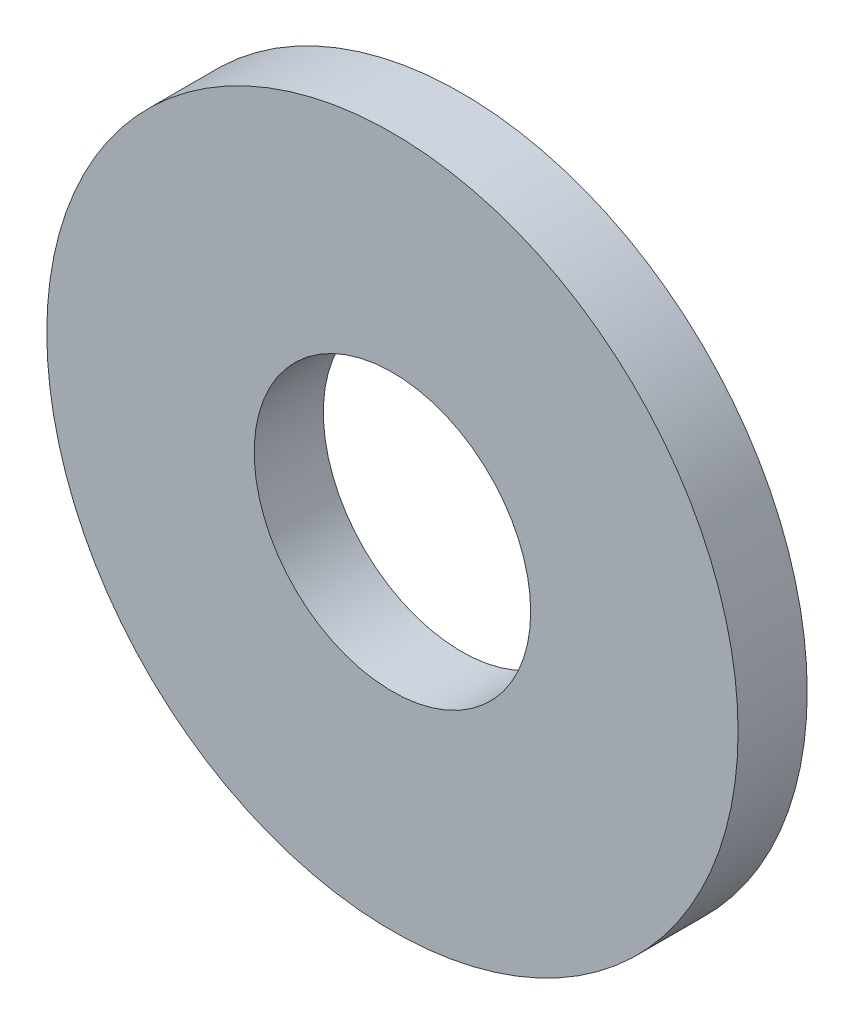
SolidWorks part; units mm, degrees
material "Nylon 6/10"
ref_plane "Front Plane" through (0, 0, 0) normal (0, 0, 1) x (1, 0, 0)
ref_plane "Top Plane" through (0, 0, 0) normal (0, 1, 0) x (1, 0, 0)
ref_plane "Right Plane" through (0, 0, 0) normal (1, 0, 0) x (0, 0, -1)
sketch "Sketch1" plane through (0, 0, 0) normal (0, 0, 1) x (1, 0, 0)
  circle A0 centre (0, 0) radius 4 construction
  circle A1 centre (0, 0) radius 1.6 construction
  point P5 (-1.6, 0)
  point P6 (1.6, 0)
  point P7 (4, 0)
  point P8 (-4, 0)
  dimension "OD" = 8
  dimension "ID" = 3.2
sketch "Sketch2" plane through (0, 0, 0) normal (1, 0, 0) x (0, 0, -1)
  line L0 (0.4, 0) -> (-0.4, 0) construction
  line L1 (0, 4) -> (0, -4) construction
  line L2 (0, 4) -> (0, -4) construction
  line L3 (0.4, 4) -> (-0.4, 4) construction
  line L4 (0.4, -4) -> (-0.4, -4) construction
  line L5 (-0.4, -4) -> (-0.4, 4) construction
  line L6 (0.4, -4) -> (0.4, 4) construction
  point P4 (0, 0)
  point P10 (0, 4)
  point P11 (-0.4, 4)
  point P14 (0, -4)
  point P15 (-0.4, -4)
  point P16 (0.4, -4)
  point P17 (0.4, 4)
  point P18 (0.4, 0)
  point P19 (-0.4, 0)
  dimension "Thickness" = 0.8
sketch "Sketch3" plane through (0, 0, 0) normal (0, 0, 1) x (1, 0, 0)
  circle A0 centre (0, 0) radius 4 construction
  circle A1 centre (0, 0) radius 1.6 construction
  circle A2 centre (0, 0) radius 4
  circle A3 centre (0, 0) radius 1.6
extrude "Boss-Extrude1" add sketch "Sketch3" along normal mid plane 0.8
equation "\"D1@Boss-Extrude1\"=\"Thickness@Sketch2\""
